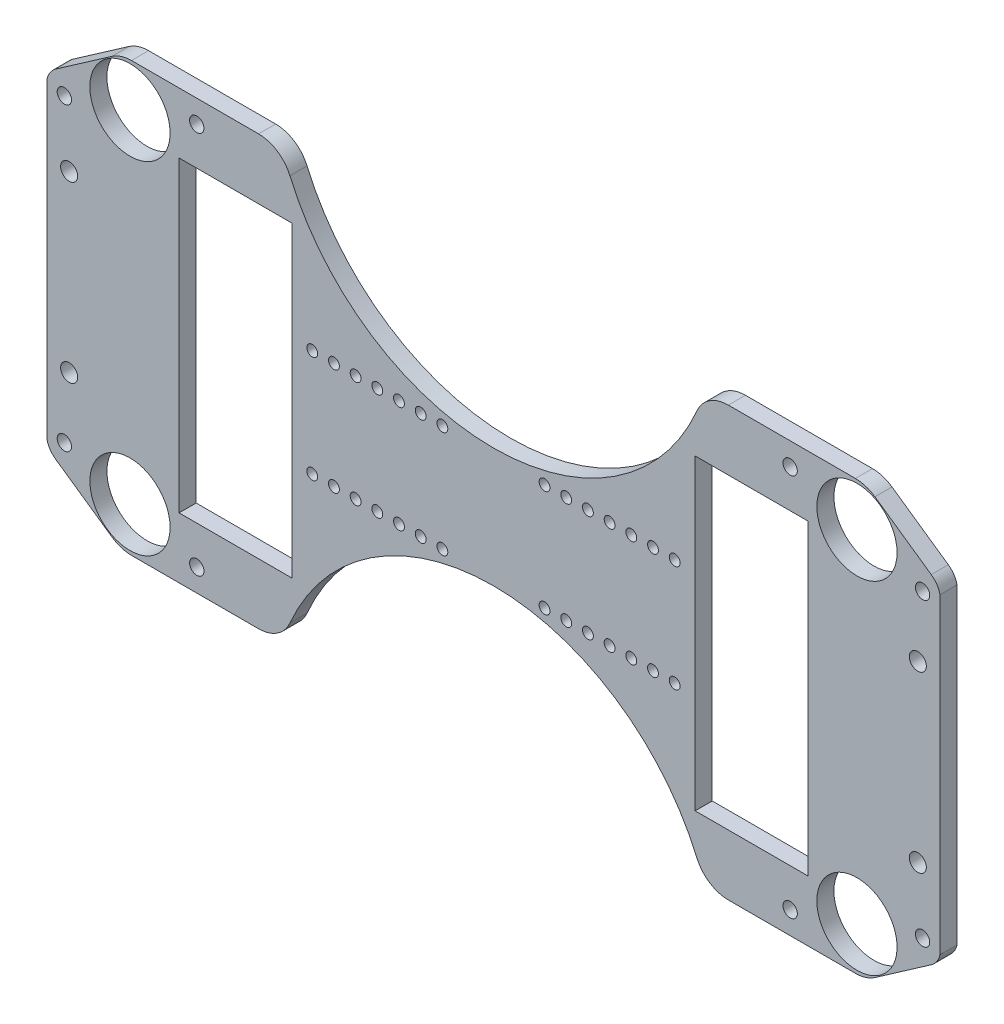
SolidWorks part; units mm, degrees
ref_plane "Front Plane" through (0, 0, 0) normal (0, 0, 1) x (1, 0, 0)
ref_plane "Top Plane" through (0, 0, 0) normal (0, 1, 0) x (1, 0, 0)
ref_plane "Right Plane" through (0, 0, 0) normal (1, 0, 0) x (0, 0, -1)
sketch "Sketch1" plane through (0, 0, 0) normal (0, 0, 1) x (1, 0, 0)
  line L0 (130.75, 0) -> (130.75, -125.5) construction
  line L1 (0, 0) -> (261.5, 0)
  line L2 (0, 0) -> (0, -125.5)
  line L3 (0, -125.5) -> (261.5, -125.5)
  line L4 (261.5, 0) -> (261.5, -125.5)
  line L9 (189.81, -17.75) -> (222.81, -17.75)
  line L10 (189.81, -17.75) -> (189.81, -107.75)
  line L11 (189.81, -107.75) -> (222.81, -107.75)
  line L12 (222.81, -17.75) -> (222.81, -107.75)
  line L13 (183.81, -62.75) -> (232.2, -62.75) construction
  line L14 (145.71, -47.125) -> (152.06, -47.125) construction
  line L15 (-22.6999, -97.9937) -> (119.2178, -142.5359) construction
  line L21 (183.81, -62.75) -> (222.81, -62.75) construction
  line L25 (145.71, -78.375) -> (152.06, -78.375) construction
  line L32 (152.06, -47.125) -> (152.06, -52.125) construction
  line L33 (164.76, -62.75) -> (164.76, -78.375) construction
  line L34 (152.06, -62.75) -> (152.06, -46.1528) construction
  line L35 (164.76, -47.125) -> (164.76, -52.125) construction
  line L36 (109.44, -62.75) -> (109.44, -46.1528) construction
  line L37 (96.74, -62.75) -> (96.74, -78.375) construction
  line L38 (177.46, -47.125) -> (177.46, -52.125) construction
  line L39 (-28.2665, -124.5) -> (107.0603, -124.5) construction
  line L41 (152.06, -47.125) -> (158.41, -47.125) construction
  line L42 (158.41, -47.125) -> (164.76, -47.125) construction
  line L43 (164.76, -47.125) -> (171.11, -47.125) construction
  line L44 (171.11, -47.125) -> (177.46, -47.125) construction
  line L45 (177.46, -47.125) -> (183.81, -47.125) construction
  line L48 (232.2, -62.75) -> (152.06, -62.75) construction
  line L52 (208.81, -17.75) -> (208.81, -107.75) construction
  line L53 (198.81, -17.75) -> (218.81, -17.75) construction
  line L54 (198.81, -17.75) -> (198.81, -107.75) construction
  line L55 (198.81, -107.75) -> (218.81, -107.75) construction
  line L56 (218.81, -17.75) -> (218.81, -107.75) construction
  line L62 (152.06, -78.375) -> (152.06, -83.375) construction
  line L65 (0, -62.75) -> (261.5, -62.75) construction
  line L71 (164.76, -78.375) -> (164.76, -83.375) construction
  line L80 (177.46, -78.375) -> (177.46, -83.375) construction
  line L87 (152.06, -62.75) -> (109.44, -62.75) construction
  line L90 (183.81, -47.125) -> (183.81, -78.375) construction
  line L93 (152.06, -47.125) -> (152.06, -62.75) construction
  line L102 (255, -37.25) -> (255, -88.25) construction
  line L103 (222.81, -62.75) -> (255, -62.75) construction
  line L106 (152.06, -78.375) -> (158.41, -78.375) construction
  line L107 (158.41, -78.375) -> (164.76, -78.375) construction
  line L108 (164.76, -78.375) -> (171.11, -78.375) construction
  line L109 (171.11, -78.375) -> (177.46, -78.375) construction
  line L110 (177.46, -78.375) -> (183.81, -78.375) construction
  line L129 (84.04, -78.375) -> (77.69, -78.375) construction
  line L130 (90.39, -78.375) -> (84.04, -78.375) construction
  line L131 (96.74, -78.375) -> (90.39, -78.375) construction
  line L132 (103.09, -78.375) -> (96.74, -78.375) construction
  line L133 (109.44, -78.375) -> (103.09, -78.375) construction
  line L134 (38.69, -62.75) -> (6.5, -62.75) construction
  line L135 (6.5, -37.25) -> (6.5, -88.25) construction
  line L136 (109.44, -47.125) -> (109.44, -62.75) construction
  line L137 (77.69, -47.125) -> (77.69, -78.375) construction
  line L139 (42.69, -17.75) -> (42.69, -107.75) construction
  line L140 (62.69, -107.75) -> (42.69, -107.75) construction
  line L141 (62.69, -17.75) -> (62.69, -107.75) construction
  line L142 (62.69, -17.75) -> (42.69, -17.75) construction
  line L143 (52.69, -17.75) -> (52.69, -107.75) construction
  line L144 (29.3, -62.75) -> (109.44, -62.75) construction
  line L147 (96.74, -47.125) -> (90.39, -47.125) construction
  line L148 (103.09, -47.125) -> (96.74, -47.125) construction
  line L150 (115.79, -78.375) -> (109.44, -78.375) construction
  line L151 (77.69, -62.75) -> (38.69, -62.75) construction
  line L153 (77.69, -62.75) -> (29.3, -62.75) construction
  line L154 (38.69, -17.75) -> (38.69, -107.75)
  line L155 (71.69, -107.75) -> (38.69, -107.75)
  line L156 (71.69, -17.75) -> (71.69, -107.75)
  line L157 (71.69, -17.75) -> (38.69, -17.75)
  circle A84 centre (255, -37.25) radius 2.5
  circle A85 centre (255, -88.25) radius 2.5
  circle A179 centre (183.81, -47.125) radius 1.59
  circle A184 centre (164.76, -78.375) radius 1.59
  circle A185 centre (152.06, -78.375) radius 1.59
  circle A196 centre (43.875, -118.8889) radius 2.1
  circle A198 centre (183.81, -78.375) radius 1.59
  circle A200 centre (145.71, -47.125) radius 1.59
  circle A201 centre (158.41, -47.125) radius 1.59
  circle A202 centre (171.11, -47.125) radius 1.59
  circle A203 centre (145.71, -78.375) radius 1.59
  circle A204 centre (158.41, -78.375) radius 1.59
  circle A205 centre (171.11, -78.375) radius 1.59
  circle A218 centre (84.04, -78.375) radius 1.59
  circle A219 centre (96.74, -78.375) radius 1.59
  circle A220 centre (109.44, -78.375) radius 1.59
  circle A221 centre (84.04, -47.125) radius 1.59
  circle A222 centre (96.74, -47.125) radius 1.59
  circle A223 centre (109.44, -47.125) radius 1.59
  circle A224 centre (90.39, -78.375) radius 1.59
  circle A225 centre (103.09, -78.375) radius 1.59
  circle A226 centre (115.79, -78.375) radius 1.59
  circle A227 centre (90.39, -47.125) radius 1.59
  circle A228 centre (103.09, -47.125) radius 1.59
  circle A229 centre (115.79, -47.125) radius 1.59
  circle A230 centre (77.69, -78.375) radius 1.59
  circle A231 centre (5.1, -106.7189) radius 2.1
  circle A232 centre (24.3158, -112.75) radius 11.75
  circle A233 centre (256.4, -106.7189) radius 2.1
  circle A234 centre (77.69, -47.125) radius 1.59
  circle A236 centre (6.5, -88.25) radius 2.5
  circle A237 centre (6.5, -37.25) radius 2.5
  circle A238 centre (237.1842, -112.75) radius 11.75
  circle A239 centre (217.625, -118.8889) radius 2.1
  circle A241 centre (152.06, -47.125) radius 1.59
  circle A242 centre (164.76, -47.125) radius 1.59
  circle A243 centre (177.46, -47.125) radius 1.59
  circle A244 centre (177.46, -78.375) radius 1.59
  circle A245 centre (256.4, -18.7811) radius 2.1
  circle A246 centre (237.1842, -12.75) radius 11.75
  circle A247 centre (217.625, -6.6111) radius 2.1
  circle A248 centre (5.1, -18.7811) radius 2.1
  circle A249 centre (43.875, -6.6111) radius 2.1
  circle A250 centre (24.3158, -12.75) radius 11.75
  point P64 (156.56, -79.5382)
  point P69 (232.2, -62.75)
  point P71 (221, -87.34)
  point P76 (233.7, -87.34)
  point P78 (221, -54.5)
  point P82 (233.7, -54.5)
  point P86 (246.4, -54.5)
  point P93 (183.81, -62.75)
  point P97 (246.4, -87.34)
  point P166 (130.75, -62.75)
  point P199 (77.69, -62.75)
  point P200 (29.3, -62.75)
  point P201 (104.94, -79.5382)
  dimension "D5" = 20
  dimension "D10" = 5
  dimension "D12" = 3.18
  dimension "D15" = 5
  dimension "D16" = 5
  dimension "D19" = 3.18
  dimension "D20" = 3.18
  dimension "D21" = 3.18
  dimension "D22" = 3.18
  dimension "D23" = 3.18
  dimension "D24" = 3.18
  dimension "D25" = 3.18
  dimension "D33" = 3.18
  dimension "D34" = 5
  dimension "D35" = 5
  dimension "D32" = 3.18
  dimension "D36" = 3.18
  dimension "D37" = 3.18
  dimension "D39" = 5.6111
  dimension "D47" = 3.18
  dimension "D49" = 3
  dimension "D51" = 20.5
  dimension "D38" = 1
  dimension "D56" = 4.2
  dimension "D50" = 23.5
  dimension "D57" = 4.2
  dimension "3,18" = 3.18
  dimension "D1" = 261.5
  dimension "D3" = 4
  dimension "D4" = 90
  dimension "D6" = 90
  dimension "D7" = 9
  dimension "D8" = 6
  dimension "D9" = 5
  dimension "D11" = 6.35
  dimension "D13" = 6.35
  dimension "D14" = 88.06
  dimension "D17" = 25.5
  dimension "D18" = 6.5
  dimension "D26" = 5
  dimension "D27" = 6.35
  dimension "D28" = 6.35
  dimension "D29" = 6.35
  dimension "D30" = 6.35
  dimension "D31" = 6.35
  dimension "D40" = 5
  dimension "D41" = 6.35
  dimension "D42" = 6.35
  dimension "D43" = 6.35
  dimension "D44" = 6.35
  dimension "D45" = 6.35
  dimension "D46" = 5
  dimension "D48" = 31.25
  dimension "D58" = 40.64
extrude "Boss-Extrude1" add sketch "Sketch1" along normal blind 5
sketch "Sketch19" plane through (0, 0, 5) normal (0, 0, 1) x (1, 0, 0)
  line L2 (130.75, 0) -> (130.75, -125.5) construction
  line L26 (0, -125.5) -> (261.5, -125.5) construction
  line L28 (2.5548, -112.2201) -> (21.6266, -125.5)
  line L35 (0, -108.3949) -> (0, -125.5)
  line L42 (261.5, 0) -> (0, 0) construction
  line L43 (0, 0) -> (0, -125.5) construction
  line L52 (0, -62.75) -> (261.5, -62.75) construction
  line L53 (261.5, -125.5) -> (261.5, 0) construction
  line L62 (21.6266, -125.5) -> (0, -125.5)
  line L63 (239.8734, -125.5) -> (261.5, -125.5)
  line L64 (261.5, -108.3949) -> (261.5, -125.5)
  line L65 (258.9452, -112.2201) -> (239.8734, -125.5)
  line L66 (258.9452, -13.2799) -> (239.8734, 0)
  line L67 (261.5, -17.1051) -> (261.5, 0)
  line L68 (239.8734, 0) -> (261.5, 0)
  line L69 (21.6266, 0) -> (0, 0)
  line L70 (0, -17.1051) -> (0, 0)
  line L71 (2.5548, -13.2799) -> (21.6266, 0)
  arc A0 (68.9051, -125.5) -> (192.5949, -125.5) centre (130.75, -145.0878) ccw
  arc A5 (117.3775, -81.542) -> (120.5525, -78.367) centre (117.3775, -78.367) ccw construction
  arc A6 (2.5548, -112.2201) -> (0, -108.3949) centre (6.1548, -107.05) cw
  arc A8 (6.1548, -100.75) -> (2.5548, -112.2201) centre (6.1548, -107.05) ccw construction
  arc A13 (192.5949, -125.5) -> (68.9051, -125.5) centre (130.75, -145.0878) ccw
  arc A20 (258.9452, -112.2201) -> (261.5, -108.3949) centre (255.3452, -107.05) ccw
  arc A21 (258.9452, -13.2799) -> (261.5, -17.1051) centre (255.3452, -18.45) cw
  arc A22 (192.5949, 0) -> (68.9051, 0) centre (130.75, 19.5878) cw
  arc A23 (2.5548, -13.2799) -> (0, -17.1051) centre (6.1548, -18.45) ccw
  arc A24 (68.9051, 0) -> (192.5949, 0) centre (130.75, 19.5878) cw
  point P14 (0, 0)
  dimension "D1" = 5
extrude "Cut-Extrude1" cut sketch "Sketch19" against normal blind 10
fillet "Fillet1" radius 10 4 edges at (192.5949, -125.5, 2.5) (68.9051, -125.5, 2.5) (68.9051, 0, 2.5) (192.5949, 0, 2.5)
fillet "Fillet2" radius 10 4 edges at (21.6266, 0, 2.5) (239.8734, 0, 2.5) (239.8734, -125.5, 2.5) (21.6266, -125.5, 2.5)
